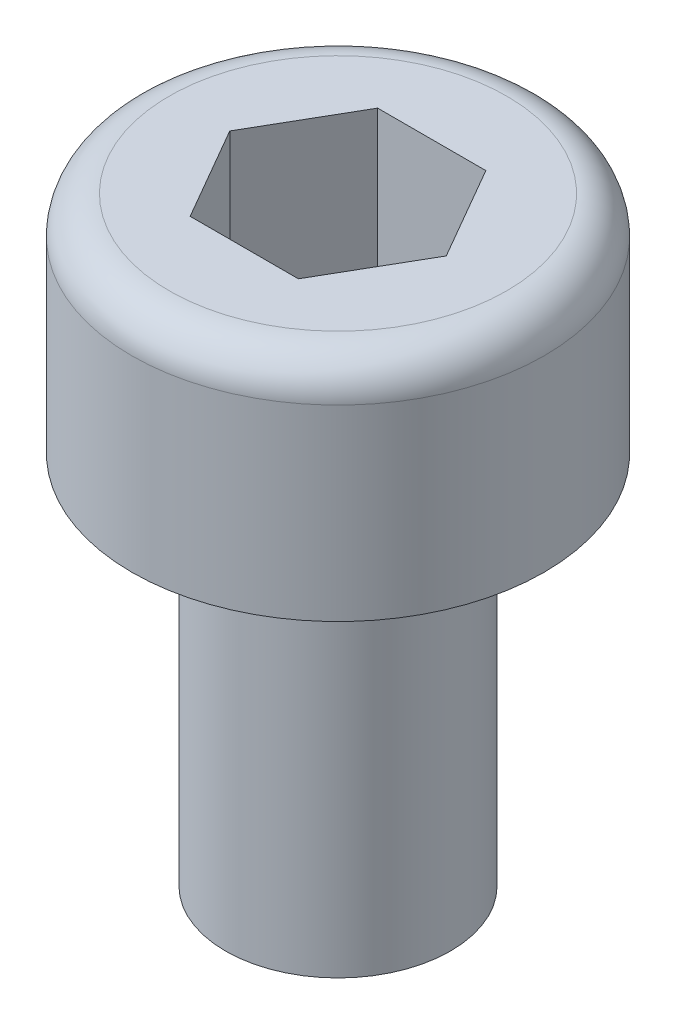
SolidWorks part; units mm, degrees
material "Alloy Steel"
ref_plane "Plane1" through (0, 0, 0) normal (0, 0, 1) x (1, 0, 0)
ref_plane "Plane2" through (0, 0, 0) normal (0, 1, 0) x (1, 0, 0)
ref_plane "Plane3" through (0, 0, 0) normal (1, 0, 0) x (0, 0, -1)
sketch "Sketch1" plane through (0, 0, 0) normal (0, 0, 1) x (1, 0, 0)
  line L0 (0, -5.4019) -> (0, 3)
  line L1 (0, 3) -> (2.25, 3)
  line L2 (2.75, 2.5) -> (2.75, 0)
  line L3 (2.75, 0) -> (1.5, 0)
  line L4 (1.5, 0) -> (1.5, -5)
  line L5 (1.5, -5) -> (0, -5.4019)
  line L6 (0, 3) -> (0, 17) construction
  arc A0 (2.25, 3) -> (2.75, 2.5) centre (2.25, 2.5) cw
  point P10 (2.75, 3)
  dimension "D6" = 0.5
  dimension "D1" = 2.75
  dimension "D2" = 3
  dimension "D3" = 1.5
  dimension "D4" = 5
  dimension "D5" = 75
revolve "Base-Revolve" add sketch "Sketch1" angle 360 about L6
sketch "Sketch2" plane through (0, 3, 0) normal (0, 1, 0) x (-1, 0, 0)
  line L1 (-1.4434, 0) -> (-0.7217, -1.25)
  line L2 (-0.7217, -1.25) -> (0.7217, -1.25)
  line L3 (0.7217, -1.25) -> (1.4434, 0)
  line L4 (1.4434, 0) -> (0.7217, 1.25)
  line L5 (0.7217, 1.25) -> (-0.7217, 1.25)
  line L6 (-0.7217, 1.25) -> (-1.4434, 0)
  circle A0 centre (0, 0) radius 1.25 construction
  dimension "D1" = 2.5
extrude "Cut-Extrude1" cut sketch "Sketch2" against normal blind 2
